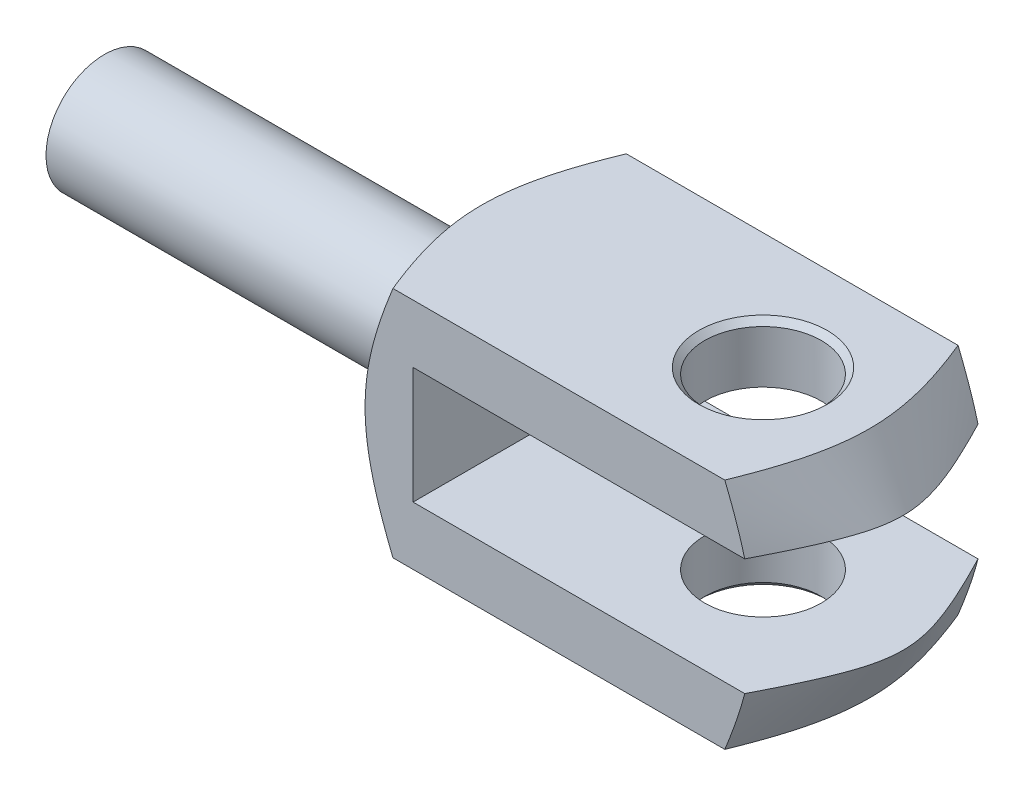
SolidWorks part; units mm, degrees
material "Plain Carbon Steel"
ref_plane "Front Plane" through (0, 0, 0) normal (0, 0, 1) x (1, 0, 0)
ref_plane "Top Plane" through (0, 0, 0) normal (0, 1, 0) x (1, 0, 0)
ref_plane "Right Plane" through (0, 0, 0) normal (1, 0, 0) x (0, 0, -1)
sketch "Sketch1" plane through (0, 0, 0) normal (1, 0, 0) x (0, 0, -1)
  circle A0 centre (0, 0) radius 5
  dimension "Thread Dia" = 10
extrude "L3" add sketch "Sketch1" along normal blind 30
sketch "Sketch6" plane through (0, 0, 0) normal (0, 0, 1) x (1, 0, 0)
  line L0 (30, -10) -> (30, 10)
  line L1 (30, -5) -> (30, 5) construction
  line L2 (30, 10) -> (69, 10)
  line L3 (69, 10) -> (69, 5)
  line L4 (69, 5) -> (37, 5)
  line L5 (37, 5) -> (37, -5)
  line L6 (-42.5614, 0) -> (42.5614, 0) construction
  line L7 (69, -5) -> (37, -5)
  line L8 (69, -10) -> (69, -5)
  line L9 (30, -10) -> (69, -10)
  line L10 (0, 5) -> (0, -5) construction
  point P12 (0, 0)
  point P13 (30, 0)
  point P14 (37, 0)
  dimension "Fork Width" = 20
  dimension "Fork Gap" = 10
  dimension "Overall Length" = 69
  dimension "L2 minus g" = 37
extrude "Claw Extrude" add sketch "Sketch6" along normal mid plane 20
sketch "Sketch8" plane through (0, 0, 0) normal (0, 1, 0) x (1, 0, 0)
  line L0 (30, 5) -> (55.9808, 50)
  line L1 (55.9808, 50) -> (30, 50)
  line L3 (-49.7253, 0) -> (49.7253, 0) construction
  line L4 (30, 5) -> (30, 50)
  line L5 (30, -10) -> (30, 10) construction
  point P6 (0, 0)
  dimension "D1" = 30
  dimension "D2" = 100
revolve "Claw Bevelling" cut sketch "Sketch8" angle 360 about L3
fillet "Thread to Claw Joining Fillet" radius 0.8 1 edges at (30, 0, 5)
sketch "Sketch11" plane through (0, 0, 0) normal (0, 0, 1) x (1, 0, 0)
  line L0 (11.265, 105) -> (69, 5)
  line L1 (69, 5) -> (69, 105)
  line L2 (69, 105) -> (11.265, 105)
  line L4 (37, 5) -> (69, 5) construction
  line L5 (69, 5) -> (69, 10) construction
  line L6 (56.2225, 0) -> (-56.2225, 0) construction
  point P22 (0, 0)
  dimension "D1" = 30
  dimension "D2" = 100
revolve "Claw Conic Taper" cut sketch "Sketch11" angle 360 about L6
sketch "Sketch9" plane through (0, 10, 0) normal (0, 1, 0) x (1, 0, 0)
  line L0 (-20.8977, 0) -> (20.8977, 0) construction
  line L1 (0, 5) -> (0, -5) construction
  circle A0 centre (57, 0) radius 5
  point P5 (0, 0)
  dimension "Hole Dia" = 10
  dimension "L2" = 57
extrude "Clevis Hole" cut sketch "Sketch9" against normal through all both and the other way through all
chamfer "Clevis Hole Chamfer" distance 0.5 angle 45 2 edges at (62, 10, 0) (57, -10, 5)
thread "M12 x 1.75" [suppressed] start angle 0, offset 3.5, length 30, pitch 1.75, diameter 12
ref_plane "Plane20" through (-3.5, 0, -6) normal (0, -1, 0) x (0, 0, -1)
sketch "Thread Profile10" [suppressed] plane through (-3.5, 0, -6) normal (0, -1, 0) x (0, 0, -1)
  line L0 (0, 0) -> (0, 1.75) construction
  line L11 (0, 0) -> (0, 1.5312)
  line L12 (0, 1.5312) -> (-0.9472, 0.9844)
  line L13 (-0.9472, 0.9844) -> (-0.9472, 0.5469)
  line L15 (-0.9472, 0.5469) -> (0, 0)
  line L17 (-0.9472, 0.7656) -> (0, 0.7656) construction
  point P2 (0, 0)
  dimension "Pitch" = 1.75
  dimension "Profile_Angle" = 60
  dimension "Profile_Land" = 0.4375
  dimension "Profile_Height" = 0.9472
ref_plane "Plane21" [suppressed] through (31.531, 0, 0) normal (1, 0, 0) x (0, 0, -1)
sketch "Sketch36" [suppressed] plane through (31.531, 0, 0) normal (1, 0, 0) x (0, 0, -1)
  circle A0 centre (0, 0) radius 6
  circle A1 centre (0, 0) radius 6 construction
sketch "Sketch37" [suppressed] plane through (0, -0.0002, 0.0003) normal (0, 0.6235, -0.7818) x (-1, 0, 0)
  line L4 (-29.9998, -6) -> (-30.5467, -5.0528)
  line L5 (-30.5467, -5.0528) -> (-30.9842, -5.0528)
  line L6 (-30.9842, -5.0528) -> (-31.531, -6)
  line L7 (-31.531, -6) -> (-29.9998, -6)
  line L8 (-29.9998, -6) -> (-30.5467, -5.0528)
  line L9 (-30.5467, -5.0528) -> (-30.9842, -5.0528)
  line L10 (-30.9842, -5.0528) -> (-31.531, -6)
  line L11 (-31.531, -6) -> (-29.9998, -6)
  dimension "D1" = 0
sweep "Cut-Sweep9" [suppressed] cut profiles "Sketch37" path "Sketch36"
thread "M10 (LH)" [suppressed] start angle 0, offset 3, length 25, pitch 1.5, diameter 10
ref_plane "Plane18" through (-3, 0, -5) normal (0, -1, 0) x (0, 0, -1)
sketch "Thread Profile9" [suppressed] plane through (-3, 0, -5) normal (0, -1, 0) x (0, 0, -1)
  line L0 (0, 0) -> (0, 1.5) construction
  line L11 (0, 0) -> (0, 1.3125)
  line L12 (0, 1.3125) -> (-0.8119, 0.8437)
  line L13 (-0.8119, 0.8437) -> (-0.8119, 0.4687)
  line L15 (-0.8119, 0.4687) -> (0, 0)
  line L17 (-0.8119, 0.6562) -> (0, 0.6562) construction
  point P2 (0, 0)
  dimension "Pitch" = 1.5
  dimension "Profile_Angle" = 60
  dimension "Profile_Land" = 0.375
  dimension "Profile_Height" = 0.8119
ref_plane "Plane19" [suppressed] through (26.3118, 0, 0) normal (1, 0, 0) x (0, 0, -1)
sketch "Sketch32" [suppressed] plane through (0, 0.0007, -0.0012) normal (-0.0001, -0.5, 0.866) x (1, 0, 0)
  line L4 (24.9993, 5) -> (25.468, 4.1881)
  line L5 (25.468, 4.1881) -> (25.843, 4.1881)
  line L6 (25.843, 4.1881) -> (26.3118, 5)
  line L7 (26.3118, 5) -> (24.9993, 5)
  line L8 (24.9993, 5) -> (25.468, 4.1881)
  line L9 (25.468, 4.1881) -> (25.843, 4.1881)
  line L10 (25.843, 4.1881) -> (26.3118, 5)
  line L11 (26.3118, 5) -> (24.9993, 5)
  dimension "D1" = 0
sketch "Sketch33" [suppressed] plane through (26.3118, 0, 0) normal (1, 0, 0) x (0, 0, -1)
  circle A0 centre (0, 0) radius 5
  circle A1 centre (0, 0) radius 5 construction
sweep "Cut-Sweep8" [suppressed] cut profiles "Sketch32" path "Sketch33"
thread "M6" [suppressed] pitch 1 start angle 0, offset 1, length 15, pitch 1, diameter 6
ref_plane "Plane3" through (-1, 0, -3) normal (0, -1, 0) x (0, 0, -1)
sketch "Thread Profile1" [suppressed] plane through (-1, 0, -3) normal (0, -1, 0) x (0, 0, -1)
  line L0 (0, 0) -> (0, 1) construction
  line L11 (0, 0) -> (0, 0.875)
  line L12 (0, 0.875) -> (-0.5413, 0.5625)
  line L13 (-0.5413, 0.5625) -> (-0.5413, 0.3125)
  line L15 (-0.5413, 0.3125) -> (0, 0)
  line L17 (-0.5413, 0.4375) -> (0, 0.4375) construction
  point P2 (0, 0)
  dimension "Pitch" = 1
  dimension "Profile_Angle" = 60
  dimension "Profile_Land" = 0.25
  dimension "Profile_Height" = 0.5413
ref_plane "Plane9" [suppressed] through (15.875, 0, 0) normal (1, 0, 0) x (0, 0, -1)
sketch "Sketch12" [suppressed] plane through (0, 0, 0) normal (0, -1, 0) x (1, 0, 0)
  line L4 (15.3125, -2.4587) -> (15, -3)
  line L5 (15, -3) -> (15.875, -3)
  line L6 (15.875, -3) -> (15.5625, -2.4587)
  line L7 (15.5625, -2.4587) -> (15.3125, -2.4587)
  line L8 (15.3125, -2.4587) -> (15, -3)
  line L9 (15, -3) -> (15.875, -3)
  line L10 (15.875, -3) -> (15.5625, -2.4587)
  line L11 (15.5625, -2.4587) -> (15.3125, -2.4587)
  dimension "D1" = 0
sketch "Sketch15" [suppressed] plane through (15.875, 0, 0) normal (1, 0, 0) x (0, 0, -1)
  circle A0 centre (0, 0) radius 3
  circle A2 centre (0, 0) radius 3 construction
sweep "Cut-Sweep2" [suppressed] cut profiles "Sketch12" path "Sketch15"
thread "M8" [suppressed] pitch 1.25 start angle 0, offset 5, length 20, pitch 1.25, diameter 8
ref_plane "Plane5" through (-5, 0, -4) normal (0, -1, 0) x (0, 0, -1)
sketch "Thread Profile3" [suppressed] plane through (-5, 0, -4) normal (0, -1, 0) x (0, 0, -1)
  line L0 (0, 0) -> (0, 1.25) construction
  line L11 (0, 0) -> (0, 1.0937)
  line L12 (0, 1.0937) -> (-0.6766, 0.7031)
  line L13 (-0.6766, 0.7031) -> (-0.6766, 0.3906)
  line L15 (-0.6766, 0.3906) -> (0, 0)
  line L17 (-0.6766, 0.5469) -> (0, 0.5469) construction
  point P2 (0, 0)
  dimension "Pitch" = 1.25
  dimension "Profile_Angle" = 60
  dimension "Profile_Land" = 0.3125
  dimension "Profile_Height" = 0.6766
ref_plane "Plane10" [suppressed] through (21.0937, 0, 0) normal (-1, 0, 0) x (0, 0, 1)
sketch "Sketch16" [suppressed] plane through (21.0937, 0, 0) normal (-1, 0, 0) x (0, 0, 1)
  circle A0 centre (0, 0) radius 4
  circle A1 centre (0, 0) radius 4 construction
sketch "Sketch17" [suppressed] plane through (0, 0, 0) normal (0, -1, 0) x (1, 0, 0)
  line L4 (20.3906, -3.3234) -> (20, -4)
  line L5 (20, -4) -> (21.0937, -4)
  line L6 (21.0937, -4) -> (20.7031, -3.3234)
  line L7 (20.7031, -3.3234) -> (20.3906, -3.3234)
  line L8 (20.3906, -3.3234) -> (20, -4)
  line L9 (20, -4) -> (21.0937, -4)
  line L10 (21.0937, -4) -> (20.7031, -3.3234)
  line L11 (20.7031, -3.3234) -> (20.3906, -3.3234)
  dimension "D1" = 0
sweep "Cut-Sweep3" [suppressed] cut profiles "Sketch17" path "Sketch16"
thread "M10" [suppressed] pitch 1.5 start angle 0, offset 5, length 25, pitch 1.5, diameter 10
ref_plane "Plane6" through (-5, 0, -5) normal (0, -1, 0) x (0, 0, -1)
sketch "Thread Profile4" [suppressed] plane through (-5, 0, -5) normal (0, -1, 0) x (0, 0, -1)
  line L0 (0, 0) -> (0, 1.5) construction
  line L11 (0, 0) -> (0, 1.3125)
  line L12 (0, 1.3125) -> (-0.8119, 0.8437)
  line L13 (-0.8119, 0.8437) -> (-0.8119, 0.4687)
  line L15 (-0.8119, 0.4687) -> (0, 0)
  line L17 (-0.8119, 0.6562) -> (0, 0.6562) construction
  point P2 (0, 0)
  dimension "Pitch" = 1.5
  dimension "Profile_Angle" = 60
  dimension "Profile_Land" = 0.375
  dimension "Profile_Height" = 0.8119
ref_plane "Plane11" [suppressed] through (26.3125, 0, 0) normal (1, 0, 0) x (0, 0, -1)
sketch "Sketch18" [suppressed] plane through (0, 0, 0) normal (0, -1, 0) x (1, 0, 0)
  line L4 (25.4687, -4.1881) -> (25, -5)
  line L5 (25, -5) -> (26.3125, -5)
  line L6 (26.3125, -5) -> (25.8437, -4.1881)
  line L7 (25.8437, -4.1881) -> (25.4687, -4.1881)
  line L8 (25.4687, -4.1881) -> (25, -5)
  line L9 (25, -5) -> (26.3125, -5)
  line L10 (26.3125, -5) -> (25.8437, -4.1881)
  line L11 (25.8437, -4.1881) -> (25.4687, -4.1881)
  dimension "D1" = 0
sketch "Sketch19" [suppressed] plane through (26.3125, 0, 0) normal (1, 0, 0) x (0, 0, -1)
  circle A0 centre (0, 0) radius 5
  circle A1 centre (0, 0) radius 5 construction
sweep "Cut-Sweep4" [suppressed] cut profiles "Sketch18" path "Sketch19"
thread "M12" [suppressed] pitch 1.75 start angle 0, offset 5, length 30, pitch 1.75, diameter 12
ref_plane "Plane7" through (-5, 0, -6) normal (0, -1, 0) x (0, 0, -1)
sketch "Thread Profile5" [suppressed] plane through (-5, 0, -6) normal (0, -1, 0) x (0, 0, -1)
  line L0 (0, 0) -> (0, 1.75) construction
  line L11 (0, 0) -> (0, 1.5312)
  line L12 (0, 1.5312) -> (-0.9472, 0.9844)
  line L13 (-0.9472, 0.9844) -> (-0.9472, 0.5469)
  line L15 (-0.9472, 0.5469) -> (0, 0)
  line L17 (-0.9472, 0.7656) -> (0, 0.7656) construction
  point P2 (0, 0)
  dimension "Pitch" = 1.75
  dimension "Profile_Angle" = 60
  dimension "Profile_Land" = 0.4375
  dimension "Profile_Height" = 0.9472
ref_plane "Plane12" [suppressed] through (31.5312, 0, 0) normal (1, 0, 0) x (0, 0, -1)
sketch "Sketch20" [suppressed] plane through (0, 0, 0) normal (0, -1, 0) x (1, 0, 0)
  line L4 (30.5469, -5.0528) -> (30, -6)
  line L5 (30, -6) -> (31.5312, -6)
  line L6 (31.5312, -6) -> (30.9844, -5.0528)
  line L7 (30.9844, -5.0528) -> (30.5469, -5.0528)
  line L8 (30.5469, -5.0528) -> (30, -6)
  line L9 (30, -6) -> (31.5312, -6)
  line L10 (31.5312, -6) -> (30.9844, -5.0528)
  line L11 (30.9844, -5.0528) -> (30.5469, -5.0528)
  dimension "D1" = 0
sketch "Sketch21" [suppressed] plane through (31.5312, 0, 0) normal (1, 0, 0) x (0, 0, -1)
  circle A0 centre (0, 0) radius 6
  circle A1 centre (0, 0) radius 6 construction
sweep "Cut-Sweep5" [suppressed] cut profiles "Sketch20" path "Sketch21"
thread "M6 (LH)" [suppressed] start angle 0, offset 1, length 15, pitch 1, diameter 6
ref_plane "Plane14" through (-1, 0, -3) normal (0, -1, 0) x (0, 0, -1)
sketch "Thread Profile7" [suppressed] plane through (-1, 0, -3) normal (0, -1, 0) x (0, 0, -1)
  line L0 (0, 0) -> (0, 1) construction
  line L11 (0, 0) -> (0, 0.875)
  line L12 (0, 0.875) -> (-0.5413, 0.5625)
  line L13 (-0.5413, 0.5625) -> (-0.5413, 0.3125)
  line L15 (-0.5413, 0.3125) -> (0, 0)
  line L17 (-0.5413, 0.4375) -> (0, 0.4375) construction
  point P2 (0, 0)
  dimension "Pitch" = 1
  dimension "Profile_Angle" = 60
  dimension "Profile_Land" = 0.25
  dimension "Profile_Height" = 0.5413
ref_plane "Plane15" [suppressed] through (15.875, 0, 0) normal (1, 0, 0) x (0, 0, -1)
sketch "Sketch24" [suppressed] plane through (15.875, 0, 0) normal (1, 0, 0) x (0, 0, -1)
  circle A0 centre (0, 0) radius 3
  circle A1 centre (0, 0) radius 3 construction
sketch "Sketch25" [suppressed] plane through (0, 0, 0) normal (0, 1, 0) x (1, 0, 0)
  line L9 (15, 3) -> (15.3125, 2.4587)
  line L10 (15.3125, 2.4587) -> (15.5625, 2.4587)
  line L11 (15.5625, 2.4587) -> (15.875, 3)
  line L12 (15.875, 3) -> (15, 3)
  line L13 (15, 3) -> (15.3125, 2.4587)
  line L14 (15.3125, 2.4587) -> (15.5625, 2.4587)
  line L15 (15.5625, 2.4587) -> (15.875, 3)
  line L16 (15.875, 3) -> (15, 3)
  dimension "D1" = 0
sweep "Cut-Sweep6" [suppressed] cut profiles "Sketch25" path "Sketch24"
thread "M8 (LH)" [suppressed] start angle 0, offset 2.5, length 20, pitch 1.25, diameter 8
ref_plane "Plane16" through (-2.5, 0, -4) normal (0, -1, 0) x (0, 0, -1)
sketch "Thread Profile8" [suppressed] plane through (-2.5, 0, -4) normal (0, -1, 0) x (0, 0, -1)
  line L0 (0, 0) -> (0, 1.25) construction
  line L11 (0, 0) -> (0, 1.0937)
  line L12 (0, 1.0937) -> (-0.6766, 0.7031)
  line L13 (-0.6766, 0.7031) -> (-0.6766, 0.3906)
  line L15 (-0.6766, 0.3906) -> (0, 0)
  line L17 (-0.6766, 0.5469) -> (0, 0.5469) construction
  point P2 (0, 0)
  dimension "Pitch" = 1.25
  dimension "Profile_Angle" = 60
  dimension "Profile_Land" = 0.3125
  dimension "Profile_Height" = 0.6766
ref_plane "Plane17" [suppressed] through (21.0937, 0, 0) normal (1, 0, 0) x (0, 0, -1)
sketch "Sketch28" [suppressed] plane through (21.0937, 0, 0) normal (1, 0, 0) x (0, 0, -1)
  circle A0 centre (0, 0) radius 4
  circle A1 centre (0, 0) radius 4 construction
sketch "Sketch29" [suppressed] plane through (0, 0, 0) normal (0, 1, 0) x (1, 0, 0)
  line L4 (20, 4) -> (20.3906, 3.3234)
  line L5 (20.3906, 3.3234) -> (20.7031, 3.3234)
  line L6 (20.7031, 3.3234) -> (21.0937, 4)
  line L7 (21.0937, 4) -> (20, 4)
  line L8 (20, 4) -> (20.3906, 3.3234)
  line L9 (20.3906, 3.3234) -> (20.7031, 3.3234)
  line L10 (20.7031, 3.3234) -> (21.0937, 4)
  line L11 (21.0937, 4) -> (20, 4)
  dimension "D1" = 0
sweep "Cut-Sweep7" [suppressed] cut profiles "Sketch29" path "Sketch28"
sketch "Sketch23" plane through (0, 0, 0) normal (0, 0, 1) x (1, 0, 0)
  line L0 (0, 4.08) -> (0, 5)
  line L1 (0, 5) -> (0.5312, 5)
  line L2 (0.5312, 5) -> (0, 4.08)
  line L4 (-11.2193, 0) -> (11.2193, 0) construction
  point P18 (0, 0)
  dimension "D1" = 30
  dimension "Min Thd Diam" = 8.16
  dimension "Thd Diam" = 10
revolve "Thread End Chamf" cut sketch "Sketch23" angle 360 about L4
